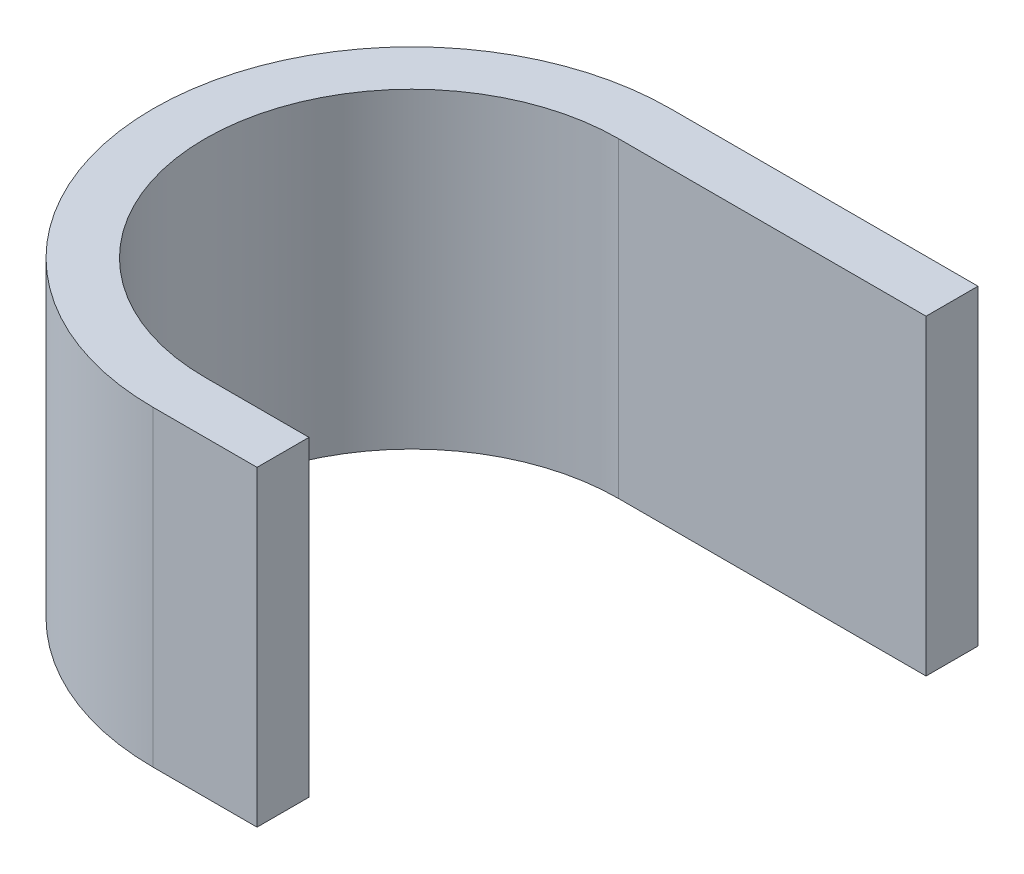
SolidWorks part; units mm, degrees
ref_plane "Front Plane" through (0, 0, 0) normal (0, 0, 1) x (1, 0, 0)
ref_plane "Top Plane" through (0, 0, 0) normal (0, 1, 0) x (1, 0, 0)
ref_plane "Right Plane" through (0, 0, 0) normal (1, 0, 0) x (0, 0, -1)
sketch "Sketch1" plane through (0, 0, 0) normal (0, 1, 0) x (1, 0, 0)
  line L3 (0, 19.9) -> (29.6, 19.9)
  line L5 (0, 24.9) -> (29.6, 24.9)
  line L6 (29.6, 19.9) -> (29.6, 24.9)
  line L7 (0, -24.9) -> (10, -24.9)
  line L9 (0, -19.9) -> (10, -19.9)
  line L10 (10, -24.9) -> (10, -19.9)
  arc A0 (0, 19.9) -> (0, -19.9) centre (0, 0) ccw
  arc A1 (0, 24.9) -> (0, -24.9) centre (0, 0) ccw
  circle A2 centre (0, 0) radius 19.9 construction
  circle A3 centre (0, 0) radius 24.9 construction
  point P11 (0, 0)
  dimension "D1" = 39.8
  dimension "D3" = 29.6
  dimension "D4" = 10
  dimension "D2" = 5
extrude "Boss-Extrude1" add sketch "Sketch1" along normal blind 30
